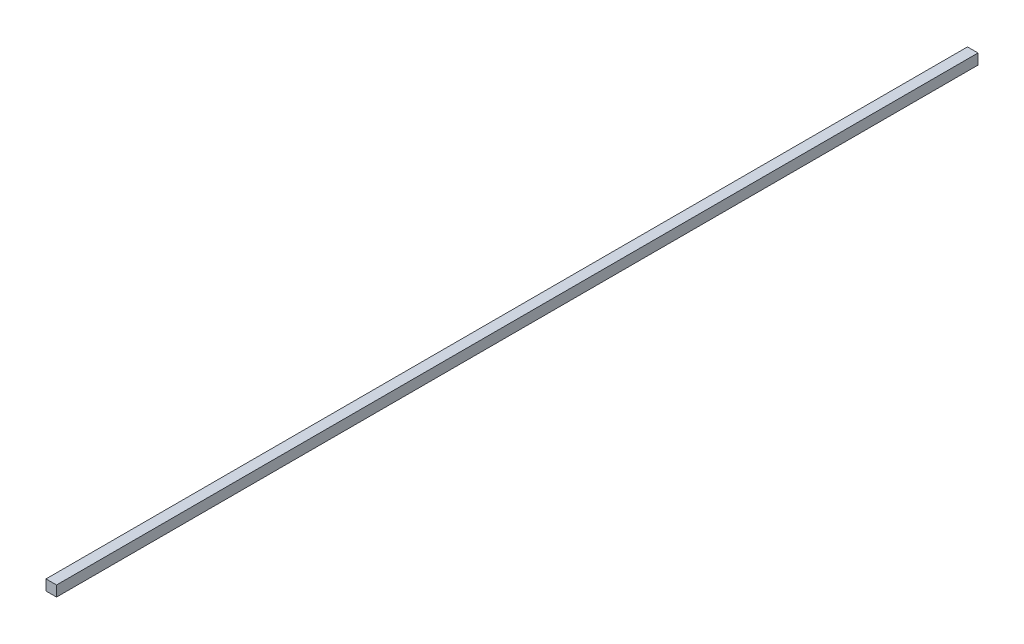
SolidWorks part; units mm, degrees
ref_plane "Front Plane" through (0, 0, 0) normal (0, 0, 1) x (1, 0, 0)
ref_plane "Top Plane" through (0, 0, 0) normal (0, 1, 0) x (1, 0, 0)
ref_plane "Right Plane" through (0, 0, 0) normal (1, 0, 0) x (0, 0, -1)
sketch "Sketch1" plane through (0, 0, 0) normal (0, 0, 1) x (1, 0, 0)
  line L7 (-2, -2) -> (2, -2)
  line L8 (-2, -2) -> (-2, 2)
  line L9 (-2, 2) -> (2, 2)
  line L10 (2, -2) -> (2, 2)
  line L11 (-2, -2) -> (2, 2) construction
  line L12 (-2, 2) -> (2, -2) construction
  point P2 (0, 2)
  point P4 (0, 0)
  point P14 (0, 0)
  dimension "Height" = 4
  dimension "Width" = 4
sketch "Sketch2" plane through (0, 0, 0) normal (1, 0, 0) x (0, 0, -1)
  line L0 (-175, 2) -> (175, 2) construction
  point P1 (-170, 2)
  point P2 (170, 2)
  point P12 (0, 2)
  dimension "Length" = 350
  dimension "D1" = 5
  dimension "D2" = 5
sketch "Sketch3" plane through (0, 0, 0) normal (0, 0, 1) x (1, 0, 0)
  line L6 (-2, 2) -> (2, 2)
  line L7 (2, 2) -> (2, -2)
  line L8 (2, -2) -> (-2, -2)
  line L9 (-2, -2) -> (-2, 2)
extrude "Boss-Extrude1" add sketch "Sketch3" along normal up to vertex (175 mm away) and the other way up to vertex (175 mm away) up to point (0, 2, 175) other way up to point (0, 2, -175)
equation "\"D1\" = \"Length@Sketch2\""
equation "\"D1@Sketch2\"=\"Width@Sketch1\"*1.25"
equation "\"D2@Sketch2\"=\"D1@Sketch2\""
